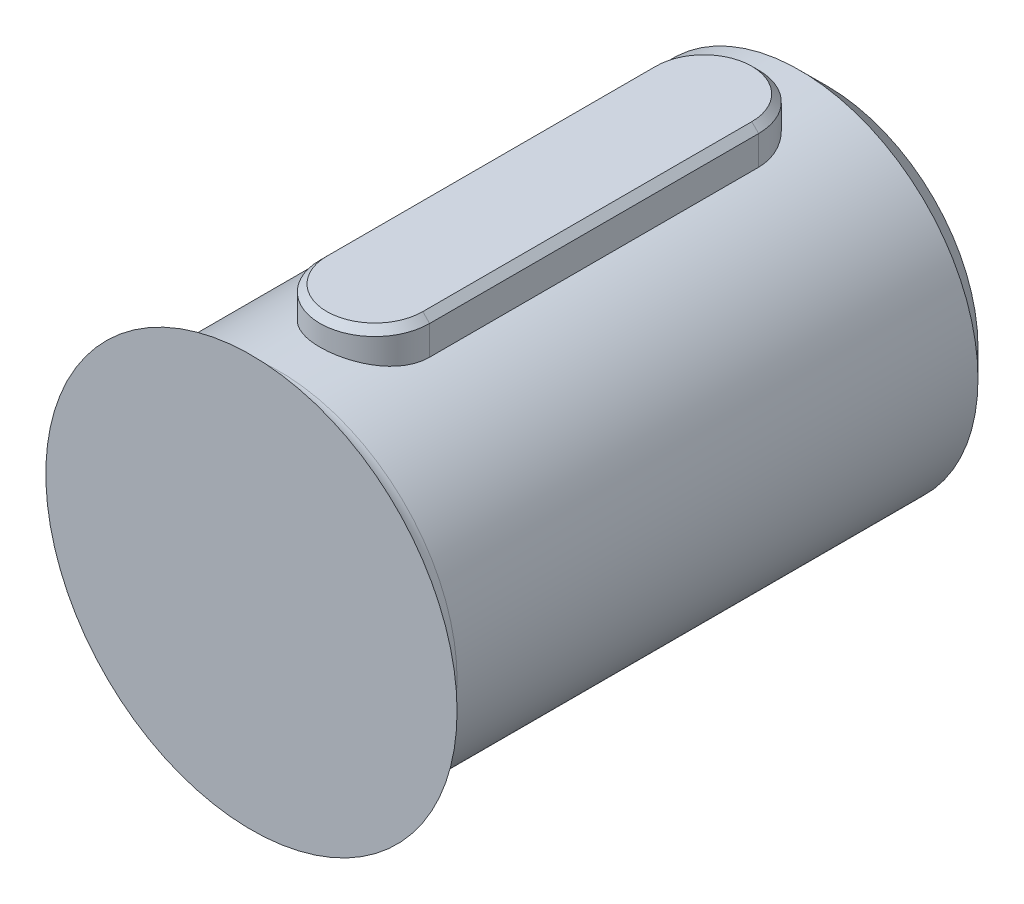
SolidWorks part; units mm, degrees
ref_plane "前视基准面" through (0, 0, 0) normal (0, 0, 1) x (1, 0, 0)
ref_plane "上视基准面" through (0, 0, 0) normal (0, 1, 0) x (1, 0, 0)
ref_plane "右视基准面" through (0, 0, 0) normal (1, 0, 0) x (0, 0, -1)
sketch "草图1" plane through (0, 0, 0) normal (0, 0, 1) x (1, 0, 0)
  circle A0 centre (0, 0) radius 41.275
  dimension "D1" = 82.55
extrude "凸台-拉伸1" add sketch "草图1" along normal blind 5
sketch "草图5" plane through (0, 0, 0) normal (0, 0, -1) x (-1, 0, 0)
  circle A0 centre (0, 0) radius 13
  dimension "D1" = 26
extrude "凸台-拉伸5" add sketch "草图5" along normal blind 42
chamfer "倒角3" distance 2 angle 45 1 edges at (-13, 0, -42)
fillet "圆角1" radius 2 1 edges at (13, 0, 0)
ref_plane "基准面2" through (0, 13, 0) normal (0, 1, 0) x (-1, 0, 0)
sketch "草图10" plane through (0, 13, 0) normal (0, 1, 0) x (-1, 0, 0)
  line L0 (0, -41.38) -> (0, -10.3796) construction
  line L3 (-4, -9) -> (-4, -33)
  line L5 (4, -9) -> (4, -33)
  arc A0 (4, -9) -> (-4, -9) centre (0, -9) ccw
  arc A1 (-4, -33) -> (4, -33) centre (0, -33) ccw
  dimension "D5" = 8
  dimension "D6" = 8
  dimension "D3" = 4
  dimension "D4" = 4
extrude "凸台-拉伸7" add sketch "草图10" along normal blind 2 and the other way up to next
chamfer "倒角4" distance 0.5 angle 45 4 edges at (4, 15, -21) (0, 15, -5) (-4, 15, -21) (0, 15, -37)
sketch "草图11" plane through (0, 0, 5) normal (0, 0, 1) x (1, 0, 0)
  circle A0 centre (0, 0) radius 65.3912
extrude "切除-拉伸1" cut sketch "草图11" against normal up to surface (5 mm away) up to face at (15, 0, 0)
